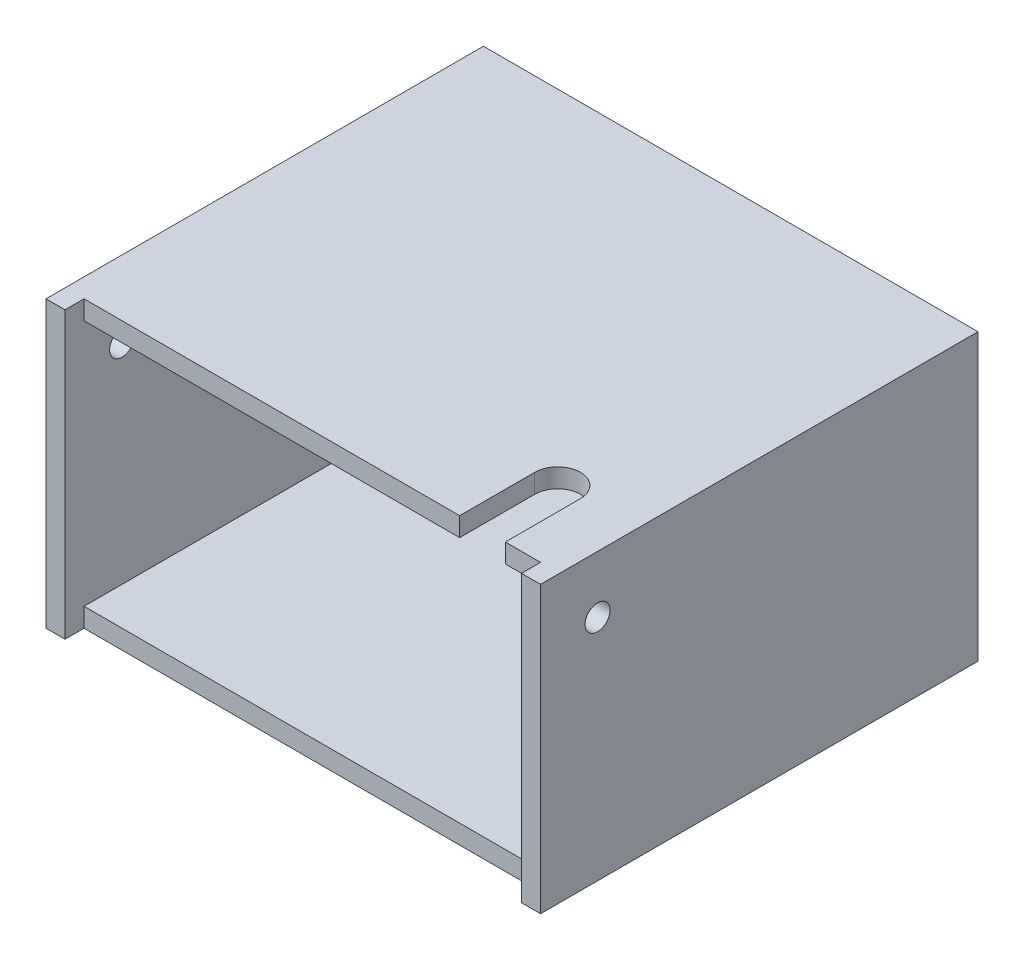
SolidWorks part; units mm, degrees
ref_plane "Front Plane" through (0, 0, 0) normal (0, 0, 1) x (1, 0, 0)
ref_plane "Top Plane" through (0, 0, 0) normal (0, 1, 0) x (1, 0, 0)
ref_plane "Right Plane" through (0, 0, 0) normal (1, 0, 0) x (0, 0, -1)
sketch "Sketch1" plane through (0, 0, 0) normal (0, 1, 0) x (1, 0, 0)
  line L1 (-38.1, -34.925) -> (38.1, -34.925)
  line L2 (-38.1, -34.925) -> (-38.1, 34.925)
  line L3 (-38.1, 34.925) -> (38.1, 34.925)
  line L4 (38.1, -34.925) -> (38.1, 34.925)
  line L5 (-38.1, -34.925) -> (38.1, 34.925) construction
  line L6 (-38.1, 34.925) -> (38.1, -34.925) construction
  point P0 (0, 0)
  dimension "D1" = 69.85
  dimension "D2" = 76.2
extrude "Boss-Extrude1" add sketch "Sketch1" along normal blind 41.275
shell "Shell2" thickness 3.175
sketch "Sketch2" plane through (0, 44.45, 0) normal (0, 1, 0) x (1, 0, 0)
  line L0 (-38.1, -34.925) -> (-38.1, -31.75)
  line L1 (-41.275, -34.925) -> (41.275, -34.925) construction
  line L2 (-38.1, -31.75) -> (38.1, -31.75)
  line L3 (38.1, -31.75) -> (38.1, -34.925)
  line L4 (-38.1, -34.925) -> (38.1, -34.925)
  line L5 (-41.275, 38.1) -> (-41.275, -34.925) construction
  line L6 (41.275, -34.925) -> (41.275, 38.1) construction
  dimension "D1" = 3.175
  dimension "D2" = 3.175
  dimension "D3" = 3.175
extrude "Cut-Extrude1" cut sketch "Sketch2" against normal through all both and the other way through all
sketch "Sketch3" plane through (0, 44.45, 0) normal (0, 1, 0) x (1, 0, 0)
  line L0 (38.1, -31.75) -> (38.1, -34.925) construction
  line L1 (-38.1, -31.75) -> (38.1, -31.75) construction
  line L2 (24.5999, -19.2151) -> (24.5999, -31.75)
  line L3 (32.2199, -19.2151) -> (32.2199, -31.75)
  line L4 (24.5999, -31.75) -> (32.2199, -31.75)
  arc A0 (32.2199, -19.2151) -> (24.5999, -19.2151) centre (28.4099, -19.2151) ccw
  dimension "D1" = 9.6901
  dimension "D3" = 7.62
  dimension "D2" = 12.5349
extrude "Cut-Extrude2" cut sketch "Sketch3" against normal up to next
sketch "Sketch4" plane through (0, 0, -34.925) normal (0, 0, 1) x (1, 0, 0)
  line L0 (38.1, 41.275) -> (38.1, 0) construction
  line L1 (38.1, 0) -> (-38.1, 0) construction
  circle A0 centre (0, 9.525) radius 2.0828
  dimension "D1" = 4.1656
  dimension "D2" = 38.1
  dimension "D3" = 9.525
extrude "Cut-Extrude3" cut sketch "Sketch4" against normal blind 3.175
sketch "Sketch5" plane through (38.1, 0, 0) normal (-1, 0, 0) x (0, 0, 1)
  line L0 (31.75, 41.275) -> (-34.925, 41.275) construction
  line L1 (34.925, 44.45) -> (34.925, -3.175) construction
  circle A0 centre (25.4, 34.925) radius 2.0828
  dimension "D1" = 4.1656
  dimension "D2" = 6.35
  dimension "D3" = 9.525
extrude "Cut-Extrude4" cut sketch "Sketch5" against normal through all both and the other way through all
